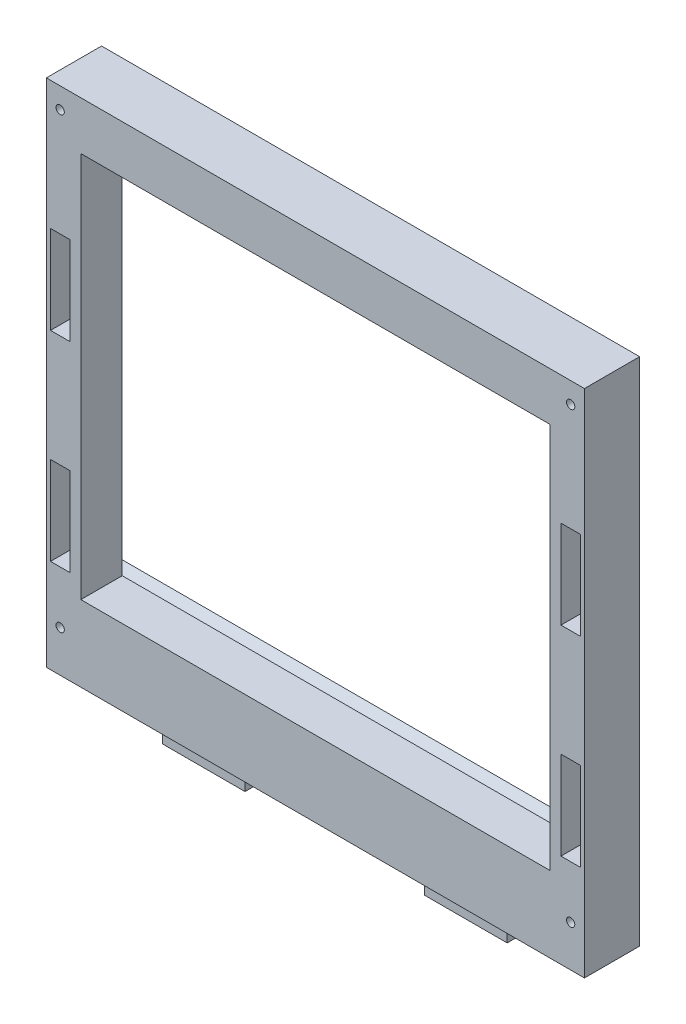
SolidWorks part; units mm, degrees
material "ABS"
ref_plane "Plano frontal" through (0, 0, 0) normal (0, 0, 1) x (1, 0, 0)
ref_plane "Plano superior" through (0, 0, 0) normal (0, 1, 0) x (1, 0, 0)
ref_plane "Plano direito" through (0, 0, 0) normal (1, 0, 0) x (0, 0, -1)
sketch "Esboço1" plane through (0, 0, 0) normal (0, 0, 1) x (1, 0, 0)
  line L1 (97.5, -92.5) -> (-97.5, -92.5)
  line L2 (97.5, -92.5) -> (97.5, 92.5)
  line L3 (97.5, 92.5) -> (-97.5, 92.5)
  line L4 (-97.5, -92.5) -> (-97.5, 92.5)
  line L5 (97.5, -92.5) -> (-97.5, 92.5) construction
  line L6 (97.5, 92.5) -> (-97.5, -92.5) construction
  point P0 (0, 0)
  dimension "D1" = 185
  dimension "D2" = 195
extrude "Ressalto-extrusão1" add sketch "Esboço1" along normal blind 20
sketch "Esboço2" plane through (0, -92.5, 0) normal (0, -1, 0) x (1, 0, 0)
  line L0 (-109.5348, 10) -> (111.1338, 10) construction
  line L1 (-97.5, 20) -> (97.5, 20) construction
  line L2 (0, 24.9881) -> (0, -34.178) construction
  line L3 (-97.5, 20) -> (-97.5, 0) construction
  line L4 (-32.5, 7) -> (-62.5, 7)
  line L5 (-32.5, 7) -> (-32.5, 13)
  line L6 (-32.5, 13) -> (-62.5, 13)
  line L7 (-62.5, 7) -> (-62.5, 13)
  line L8 (-32.5, 7) -> (-62.5, 13) construction
  line L9 (-32.5, 13) -> (-62.5, 7) construction
  line L10 (32.5, 13) -> (62.5, 7) construction
  line L11 (32.5, 7) -> (62.5, 13) construction
  line L12 (62.5, 7) -> (62.5, 13)
  line L13 (32.5, 13) -> (62.5, 13)
  line L14 (32.5, 7) -> (32.5, 13)
  line L15 (32.5, 7) -> (62.5, 7)
  point P4 (-47.5, 10)
  point P19 (47.5, 10)
  dimension "D1" = 10
  dimension "D2" = 6
  dimension "D3" = 30
  dimension "D4" = 50
extrude "Ressalto-extrusão2" add sketch "Esboço2" along normal blind 10
sketch "Esboço3" plane through (0, 0, 20) normal (0, 0, 1) x (1, 0, 0)
  line L0 (-130.8005, -6.25) -> (134.3358, -6.25) construction
  line L1 (-97.5, 92.5) -> (-97.5, -92.5) construction
  line L2 (-89, 14) -> (-96, 14)
  line L3 (-89, 14) -> (-89, 46)
  line L4 (-89, 46) -> (-96, 46)
  line L5 (-96, 14) -> (-96, 46)
  line L6 (-89, 14) -> (-96, 46) construction
  line L7 (-89, 46) -> (-96, 14) construction
  line L9 (-89, -58.5) -> (-96, -26.5) construction
  line L10 (-89, -26.5) -> (-96, -58.5) construction
  line L11 (-96, -26.5) -> (-96, -58.5)
  line L12 (-89, -58.5) -> (-96, -58.5)
  line L13 (-89, -26.5) -> (-89, -58.5)
  line L14 (-89, -26.5) -> (-96, -26.5)
  line L15 (0, 106.7871) -> (0, -117.3693) construction
  line L16 (89, -26.5) -> (96, -58.5) construction
  line L17 (89, -58.5) -> (96, -26.5) construction
  line L18 (89, -26.5) -> (96, -26.5)
  line L19 (89, -26.5) -> (89, -58.5)
  line L20 (89, -58.5) -> (96, -58.5)
  line L21 (96, -26.5) -> (96, -58.5)
  line L22 (89, 46) -> (96, 14) construction
  line L23 (89, 14) -> (96, 46) construction
  line L24 (96, 14) -> (96, 46)
  line L25 (89, 46) -> (96, 46)
  line L26 (89, 14) -> (89, 46)
  line L27 (89, 14) -> (96, 14)
  line L28 (-155.0027, 80) -> (139.2385, 80) construction
  line L29 (-97.5, -92.5) -> (97.5, -92.5) construction
  point P2 (-92.5, 30)
  point P16 (-92.5, -42.5)
  point P23 (92.5, -42.5)
  point P28 (92.5, 30)
  dimension "D1" = 32
  dimension "D2" = 7
  dimension "D3" = 1.5
  dimension "D4" = 50
  dimension "D5" = 172.5
  dimension "D6" = 86.25
extrude "Corte-extrusão1" cut sketch "Esboço3" against normal blind 10
sketch "Esboço5" plane through (0, -92.5, 0) normal (0, -1, 0) x (1, 0, 0)
  line L0 (-102.5389, 10) -> (114.9319, 10) construction
  line L2 (-97.5, 20) -> (97.5, 20) construction
  line L3 (-97.5, 20) -> (-97.5, 0) construction
  line L4 (0, 18.212) -> (0, -19.7462) construction
  circle A0 centre (-92.5, 10) radius 1.5
  circle A1 centre (92.5, 10) radius 1.5
  dimension "D2" = 3
  dimension "D1" = 10
  dimension "D3" = 5
extrude "Corte-extrusão3" cut sketch "Esboço5" against normal blind 8
sketch "Esboço6" plane through (0, 0, 0) normal (0, 0, -1) x (-1, 0, 0)
  line L0 (0, 110.3211) -> (0, -118.4678) construction
  line L1 (-131.3107, -6.25) -> (134.1127, -6.25) construction
  line L2 (97.5, -92.5) -> (-97.5, -92.5) construction
  line L3 (-97.5, -92.5) -> (-97.5, 92.5) construction
  line L4 (-97.5, 92.5) -> (97.5, 92.5) construction
  circle A0 centre (-92.5, 85) radius 1.5
  circle A1 centre (92.5, 85) radius 1.5
  circle A2 centre (-92.5, -77.5) radius 1.5
  circle A3 centre (92.5, -77.5) radius 1.5
  dimension "D2" = 3
  dimension "D3" = 5
  dimension "D4" = 7.5
  dimension "D5" = 3
  dimension "D1" = 86.25
  dimension "D6" = 5
  dimension "D7" = 15
extrude "Corte-extrusão4" cut sketch "Esboço6" against normal through all
sketch "Esboço8" plane through (0, 0, 0) normal (0, 0, -1) x (-1, 0, 0)
  line L0 (0, 100.342) -> (0, -100.3526) construction
  line L1 (-125.2567, 5) -> (132.6442, 5) construction
  line L2 (97.5, -92.5) -> (-97.5, -92.5) construction
  line L4 (85, -65) -> (-85, -65)
  line L5 (85, -65) -> (85, 75)
  line L6 (85, 75) -> (-85, 75)
  line L7 (-85, -65) -> (-85, 75)
  line L8 (85, -65) -> (-85, 75) construction
  line L9 (85, 75) -> (-85, -65) construction
  point P7 (0, 5)
  dimension "D1" = 97.5
  dimension "D2" = 140
  dimension "D3" = 170
extrude "Corte-extrusão6" cut sketch "Esboço8" against normal through all
sketch "Esboço9" plane through (-97.5, 0, 0) normal (-1, 0, 0) x (0, 0, 1)
  line L0 (-27.5071, 5) -> (51.1391, 5) construction
  line L1 (20, -92.5) -> (0, -92.5) construction
  line L2 (0, -65) -> (0, 75)
  line L3 (0, 92.5) -> (0, -92.5) construction
  line L4 (0, 75) -> (5, 78.501)
  line L5 (5, 78.501) -> (5, -68.501)
  line L6 (0, -65) -> (5, -68.501)
  point P13 (5, 5)
  point P14 (0, 5)
  dimension "D1" = 97.5
  dimension "D2" = 70
  dimension "D3" = 55
  dimension "D4" = 5
extrude "Corte-extrusão7" cut sketch "Esboço9" against normal blind 190
